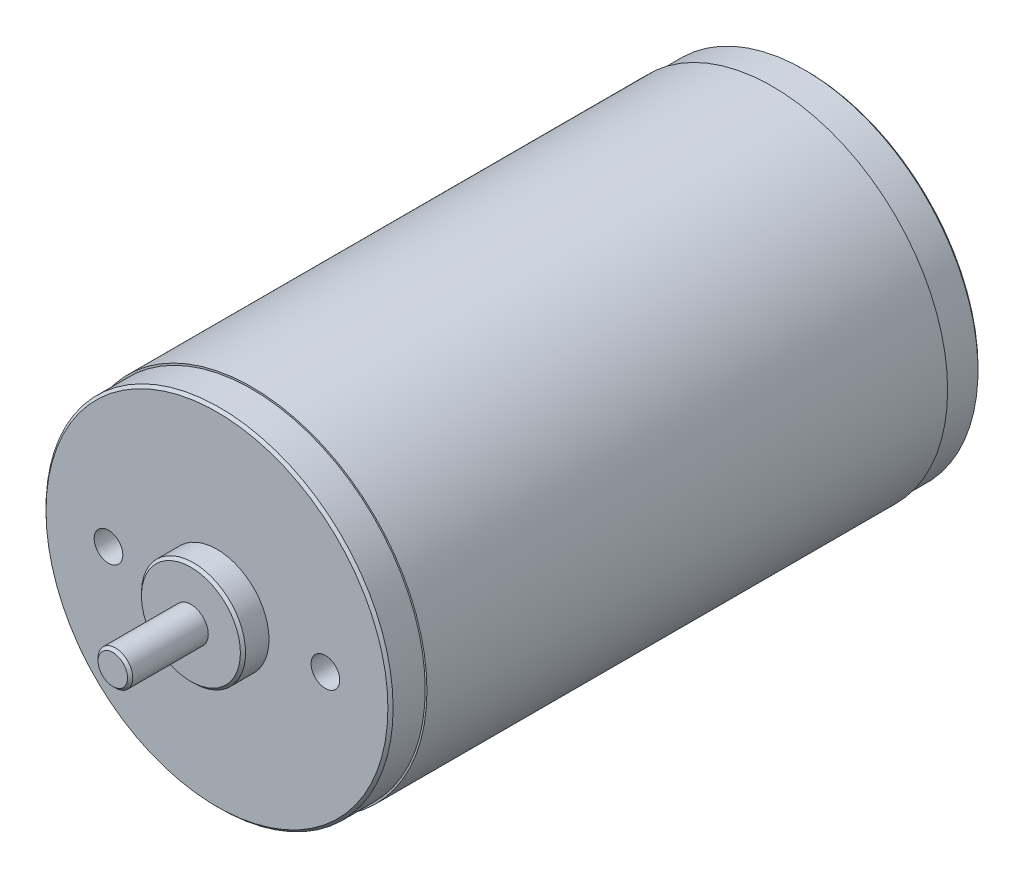
SolidWorks part; units mm, degrees
ref_plane "Front Plane" through (0, 0, 0) normal (0, 0, 1) x (1, 0, 0)
ref_plane "Top Plane" through (0, 0, 0) normal (0, 1, 0) x (1, 0, 0)
ref_plane "Right Plane" through (0, 0, 0) normal (1, 0, 0) x (0, 0, -1)
sketch "Sketch1" plane through (0, 0, 0) normal (0, 1, 0) x (1, 0, 0)
  line L0 (20.2, 64) -> (0, 64)
  line L1 (0, 64) -> (0, 4)
  line L2 (0, 4) -> (20.2, 4)
  line L3 (20.2, 4) -> (20.2, 64)
  line L4 (0, 64) -> (0, 4) construction
revolve "Revolve1" add sketch "Sketch1" angle 360 about L4
sketch "Sketch2" plane through (0, 0, -4) normal (0, 0, 1) x (1, 0, 0)
  circle A0 centre (0, 0) radius 20
extrude "Boss-Extrude1" add sketch "Sketch2" along normal blind 4
sketch "Sketch3" plane through (0, 0, 0) normal (0, 0, 1) x (1, 0, 0)
  circle A0 centre (0, 0) radius 6
extrude "Boss-Extrude2" add sketch "Sketch3" along normal blind 3
sketch "Sketch4" plane through (0, 0, 3) normal (0, 0, 1) x (1, 0, 0)
  circle A0 centre (0, 0) radius 2
extrude "Boss-Extrude3" add sketch "Sketch4" along normal blind 9
sketch "Sketch5" plane through (0, 0, -64) normal (0, 0, -1) x (-1, 0, 0)
  circle A0 centre (0, 0) radius 20
extrude "Boss-Extrude4" add sketch "Sketch5" along normal blind 4
sketch "Sketch6" plane through (0, 0, -68) normal (0, 0, -1) x (-1, 0, 0)
  circle A0 centre (0, 0) radius 6.325
extrude "Boss-Extrude5" add sketch "Sketch6" along normal blind 1.5
hole_wizard "Ø3.3 (3.3) Diameter Hole1" positions "Sketch8" profile "Sketch7" hole size "Ø3.3" standard "ANSI Metric"
sketch "Sketch8" plane through (0, 0, 0) normal (0, 0, 1) x (1, 0, 0)
  point P0 (-12.5, 0)
  point P1 (12.5, 0)
sketch "Sketch7" plane through (-12.5, 0, 0) normal (1, 0, 0) x (0, -1, 0)
  line L0 (0, 0) -> (0, 9.0914)
  line L1 (0, 9.0914) -> (1.65, 8.1)
  line L2 (1.65, 8.1) -> (1.65, 0)
  line L5 (1.65, 0) -> (0, 0)
  line L10 (0, 9.0914) -> (-1.65, 8.1) construction
  line L11 (0, -6.35) -> (0, 107.95) construction
  dimension "Hole Dia." = 3.3
  dimension "Hole Depth" = 8.1
  dimension "Drill Angle" = 118
chamfer "Chamfer1" distance 0.3 angle 45 1 edges at (2, 0, 12)
